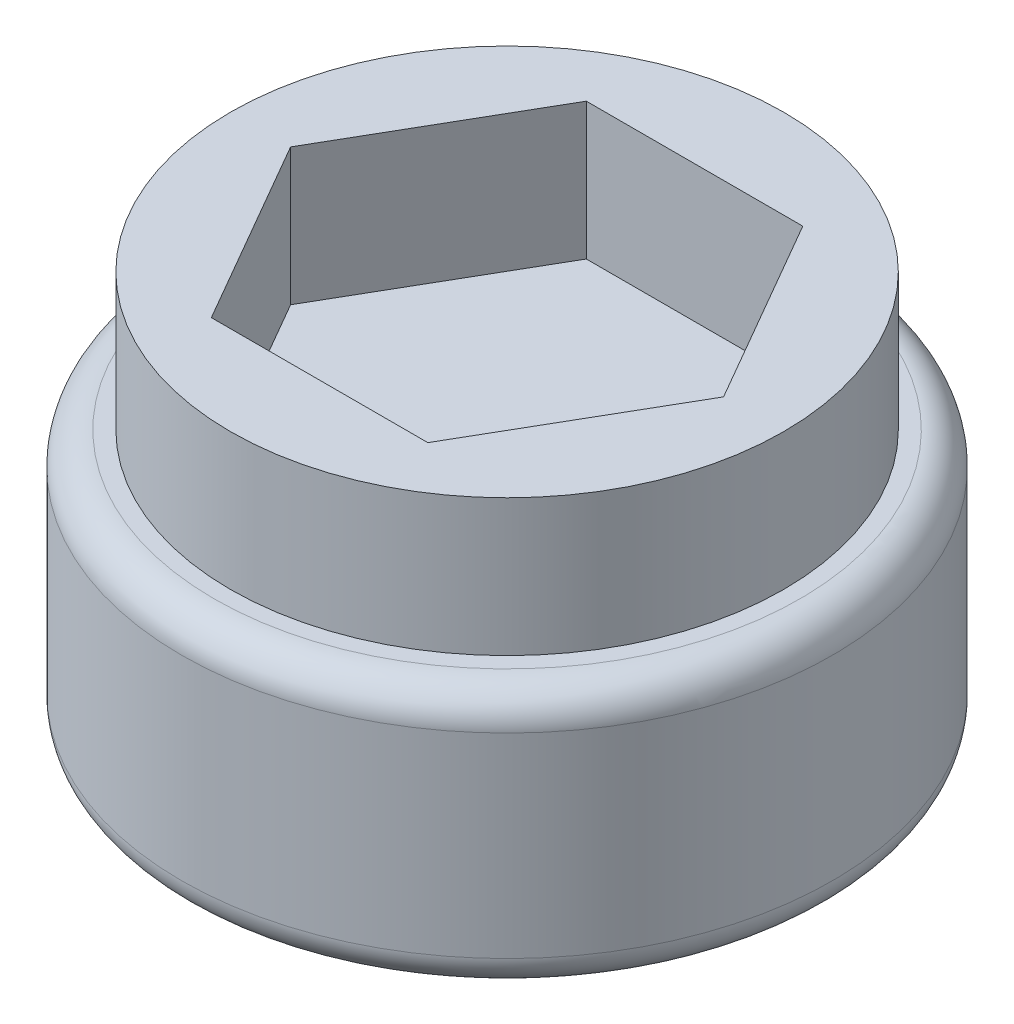
SolidWorks part; units mm, degrees
ref_plane "Front Plane" through (0, 0, 0) normal (0, 0, 1) x (1, 0, 0)
ref_plane "Top Plane" through (0, 0, 0) normal (0, 1, 0) x (1, 0, 0)
ref_plane "Right Plane" through (0, 0, 0) normal (1, 0, 0) x (0, 0, -1)
sketch "Sketch1" plane through (0, 0, 0) normal (0, 1, 0) x (1, 0, 0)
  line L1 (0.6582, 0) -> (0.3291, 0.57)
  line L2 (0.3291, 0.57) -> (-0.3291, 0.57)
  line L3 (-0.3291, 0.57) -> (-0.6582, 0)
  line L4 (-0.6582, 0) -> (-0.3291, -0.57)
  line L5 (-0.3291, -0.57) -> (0.3291, -0.57)
  line L6 (0.3291, -0.57) -> (0.6582, 0)
  circle A0 centre (0, 0) radius 0.57 construction
extrude "Boss-Extrude1" add sketch "Sketch1" along normal blind 1.75
sketch "Sketch2" plane through (0, 1.75, 0) normal (0, 1, 0) x (1, 0, 0)
  line L0 (0, 0) -> (0, -0.1986)
  line L1 (0.6582, 0) -> (0.3291, 0.57)
  line L2 (0.3291, 0.57) -> (-0.3291, 0.57)
  line L3 (-0.3291, 0.57) -> (-0.6582, 0)
  line L4 (-0.6582, 0) -> (-0.3291, -0.57)
  line L5 (-0.3291, -0.57) -> (0.3291, -0.57)
  line L6 (0.3291, -0.57) -> (0.6582, 0)
  line L7 (4.375, 0) -> (-2.1875, 3.7889) construction
  line L8 (-2.1875, 3.7889) -> (-2.1875, -3.7889) construction
  line L9 (-2.1875, -3.7889) -> (4.375, 0) construction
  line L10 (0, -0.1986) -> (0, 0.1978)
  line L11 (0, 0.1978) -> (4.375, 0)
  line L12 (4.375, 0) -> (0, -0.1986)
  circle A0 centre (0, 0) radius 0.57 construction
  circle A1 centre (0, 0) radius 4.375 construction
  line M2 (0.6582, 0) -> (0.3291, 0.57)
extrude "Boss-Extrude2" add sketch "Sketch2" along normal blind 0.5 contours L12 L11 L6 M2 | L12 L6 L11 L10 L0 M2
sketch "Sketch3" plane through (0, 1.75, 0) normal (0, 1, 0) x (1, 0, 0)
  line L0 (0.6582, 0) -> (0.3291, 0.57)
  line L1 (-0.6582, 0) -> (-0.3291, -0.57)
  line L2 (-0.3291, -0.57) -> (0.3291, -0.57)
  line L3 (0.3291, -0.57) -> (0.6582, 0)
  line L4 (0.3291, 0.57) -> (-0.3291, 0.57)
  line L5 (-0.3291, 0.57) -> (-0.6582, 0)
  circle A0 centre (0, 0) radius 0.6582 construction
extrude "Boss-Extrude5" add sketch "Sketch3" along normal blind 3.5
sketch "Sketch4" plane through (0, 5.25, 0) normal (0, 1, 0) x (1, 0, 0)
  circle A0 centre (0, 0) radius 3.5
extrude "Boss-Extrude7" add sketch "Sketch4" along normal blind 2
sketch "Sketch11" plane through (0, 1.75, 0) normal (0, -1, 0) x (-1, 0, 0)
  circle A0 centre (0, 0) radius 4.5054
  circle A1 centre (0, 0) radius 3.5
extrude "Cut-Extrude3" cut sketch "Sketch11" against normal blind 2
sketch "Sketch12" plane through (0, 0, 0) normal (0, -1, 0) x (-1, 0, 0)
  circle A0 centre (0, 0) radius 3.5
extrude "Cut-Extrude4" cut sketch "Sketch12" against normal blind 3
sketch "Sketch16" plane through (0, 3, 0) normal (0, -1, 0) x (-1, 0, 0)
  line L0 (1.1, 0) -> (-1.1, 0)
  line L1 (-1.1, 0) -> (-0.55, -0.9526)
  line L2 (-0.55, -0.9526) -> (0.55, -0.9526)
  line L3 (0.55, -0.9526) -> (1.1, 0)
  line L4 (1.1, 0) -> (0.55, 0.9526)
  line L5 (0.55, 0.9526) -> (-0.55, 0.9526)
  line L6 (-0.55, 0.9526) -> (-1.1, 0)
  circle A0 centre (0, 0) radius 0.9526 construction
  line M1 (-0.6582, 0) -> (-0.3291, -0.57)
  line M2 (-0.3291, -0.57) -> (0.3291, -0.57)
  line M3 (0.3291, -0.57) -> (0.6582, 0)
  line M4 (0.6582, 0) -> (0.3291, 0.57)
  line M5 (0.3291, 0.57) -> (-0.3291, 0.57)
  line M6 (-0.3291, 0.57) -> (-0.6582, 0)
  dimension "D1" = 2.2
extrude "Boss-Extrude8" add sketch "Sketch16" against normal blind 2.5 contours L2 L3 L0 L1 M3 M2 M1 | L5 L6 L0 L4 M6 M5 M4 | L0 M4 M5 M6 | L0 M3 M1 M2
chamfer "Chamfer1" distance 0.5 angle 30 6 edges at (0, 5.25, 0.9526) (-0.825, 5.25, 0.4763) (-0.825, 5.25, -0.4763) (0, 5.25, -0.9526) (0.825, 5.25, -0.4763) (0.825, 5.25, 0.4763)
sketch "Sketch17" plane through (0, 3, 0) normal (0, -1, 0) x (-1, 0, 0)
  line L1 (-2.9959, 0) -> (-1.498, -2.5945)
  line L2 (-1.498, -2.5945) -> (1.498, -2.5945)
  line L3 (1.498, -2.5945) -> (2.9959, 0)
  line L4 (2.9959, 0) -> (1.498, 2.5945)
  line L5 (1.498, 2.5945) -> (-1.498, 2.5945)
  line L6 (-1.498, 2.5945) -> (-2.9959, 0)
  circle A0 centre (0, 0) radius 2.5945 construction
  circle A1 centre (0, 0) radius 3.25
extrude "Boss-Extrude9" add sketch "Sketch17" against normal blind 3
sketch "Sketch18" plane through (0, 3, 0) normal (0, -1, 0) x (-1, 0, 0)
  circle A0 centre (0, 0) radius 1.7681
extrude "Cut-Extrude8" cut sketch "Sketch18" against normal blind 2.25
sketch "Sketch20" plane through (0, 7.25, 0) normal (0, 1, 0) x (1, 0, 0)
  circle A0 centre (0, 0) radius 5
extrude "Boss-Extrude10" add sketch "Sketch20" against normal blind 2
sketch "Sketch21" plane through (0, 7.25, 0) normal (0, 1, 0) x (1, 0, 0)
  circle A0 centre (0, 0) radius 5
extrude "Boss-Extrude11" add sketch "Sketch21" along normal blind 2
fillet "Fillet1" radius 0.5 2 edges at (0, 5.25, 5) (0, 9.25, 5)
sketch "Sketch25" plane through (0, 5.25, 0) normal (0, -1, 0) x (-1, 0, 0)
  circle A0 centre (0, 0) radius 4.0004
extrude "Cut-Extrude9" cut sketch "Sketch25" along normal blind 10
sketch "Sketch26" plane through (0, 9.25, 0) normal (0, 1, 0) x (1, 0, 0)
  line L0 (0, 0) -> (2.4942, 1.44)
  line L1 (3.3255, 0) -> (1.6628, 2.88)
  line L2 (1.6628, 2.88) -> (-1.6628, 2.88)
  line L3 (-1.6628, 2.88) -> (-3.3255, 0)
  line L4 (-3.3255, 0) -> (-1.6628, -2.88)
  line L5 (-1.6628, -2.88) -> (1.6628, -2.88)
  line L6 (1.6628, -2.88) -> (3.3255, 0)
  circle A0 centre (0, 0) radius 4.25
  circle A1 centre (0, 0) radius 2.88 construction
  dimension "D1" = 8.5
  dimension "D2" = 2.88
extrude "Boss-Extrude12" add sketch "Sketch26" along normal blind 2.1 contours A0 L6 L5 L4 L3 L2 L1
